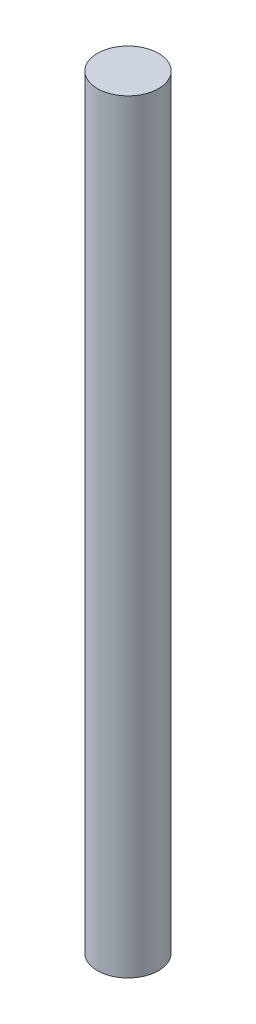
SolidWorks part; units mm, degrees
ref_plane "Front Plane" through (0, 0, 0) normal (0, 0, 1) x (1, 0, 0)
ref_plane "Top Plane" through (0, 0, 0) normal (0, 1, 0) x (1, 0, 0)
ref_plane "Right Plane" through (0, 0, 0) normal (1, 0, 0) x (0, 0, -1)
sketch "Sketch1" plane through (0, 0, 0) normal (0, 1, 0) x (1, 0, 0)
  circle A0 centre (0, 0) radius 20
extrude "Boss-Extrude1" add sketch "Sketch1" along normal blind 500
